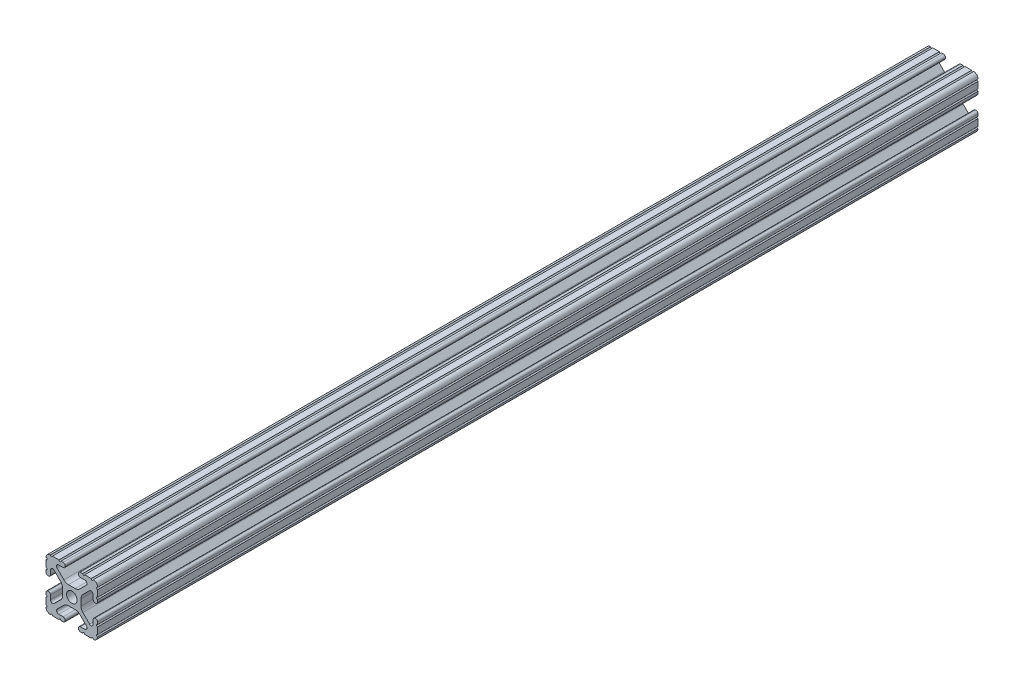
SolidWorks part; units mm, degrees
ref_plane "Front Plane" through (0, 0, 0) normal (0, 0, 1) x (1, 0, 0)
ref_plane "Top Plane" through (0, 0, 0) normal (0, 1, 0) x (1, 0, 0)
ref_plane "Right Plane" through (0, 0, 0) normal (1, 0, 0) x (0, 0, -1)
sketch "Sketch1" plane through (0, 0, 0) normal (0, 0, 1) x (1, 0, 0)
  line L88 (-7.1797, -8.6452) -> (-3.9523, -5.4237)
  line L89 (-1.7093, -4.4958) -> (1.7093, -4.4958)
  line L90 (3.9523, -5.4237) -> (7.1797, -8.6452)
  line L91 (6.4164, -10.4902) -> (4.2875, -10.4902)
  line L92 (3.2385, -11.5392) -> (3.2385, -11.651)
  line L93 (4.2875, -12.7) -> (5.3171, -12.7)
  line L94 (6.3331, -12.7) -> (9.5504, -12.7)
  line L95 (12.7, -9.5504) -> (12.7, -6.3331)
  line L96 (12.7, -5.3171) -> (12.7, -4.2875)
  line L97 (11.651, -3.2385) -> (11.5392, -3.2385)
  line L98 (10.4902, -4.2875) -> (10.4902, -6.4021)
  line L99 (8.7371, -7.1294) -> (5.441, -3.8408)
  line L100 (4.5085, -1.5932) -> (4.5085, 1.5932)
  line L101 (5.441, 3.8408) -> (8.7371, 7.1294)
  line L102 (10.4902, 6.4021) -> (10.4902, 4.2875)
  line L103 (11.5392, 3.2385) -> (11.651, 3.2385)
  line L104 (12.7, 4.2875) -> (12.7, 5.3171)
  line L105 (12.7, 6.3331) -> (12.7, 9.5504)
  line L106 (9.5504, 12.7) -> (6.3331, 12.7)
  line L107 (5.3171, 12.7) -> (4.2875, 12.7)
  line L108 (3.2385, 11.651) -> (3.2385, 11.5392)
  line L109 (4.2875, 10.4902) -> (6.4768, 10.4902)
  line L110 (7.207, 8.7244) -> (3.8983, 5.4232)
  line L111 (1.6558, 4.4958) -> (-1.6558, 4.4958)
  line L112 (-3.8983, 5.4232) -> (-7.207, 8.7244)
  line L113 (-6.4768, 10.4902) -> (-4.2875, 10.4902)
  line L114 (-3.2385, 11.5392) -> (-3.2385, 11.651)
  line L115 (-4.2875, 12.7) -> (-5.3171, 12.7)
  line L116 (-6.3331, 12.7) -> (-9.5504, 12.7)
  line L117 (-12.7, 9.5504) -> (-12.7, 6.3331)
  line L118 (-12.7, 5.3171) -> (-12.7, 4.2875)
  line L119 (-11.651, 3.2385) -> (-11.5392, 3.2385)
  line L120 (-10.4902, 4.2875) -> (-10.4902, 6.4021)
  line L121 (-8.7371, 7.1294) -> (-5.441, 3.8408)
  line L122 (-4.5085, 1.5932) -> (-4.5085, -1.5932)
  line L123 (-5.441, -3.8408) -> (-8.7371, -7.1294)
  line L124 (-10.4902, -6.4021) -> (-10.4902, -4.2875)
  line L125 (-11.5392, -3.2385) -> (-11.651, -3.2385)
  line L126 (-12.7, -4.2875) -> (-12.7, -5.3171)
  line L127 (-12.7, -6.3331) -> (-12.7, -9.5504)
  line L128 (-9.5504, -12.7) -> (-6.3331, -12.7)
  line L129 (-5.3171, -12.7) -> (-4.2875, -12.7)
  line L130 (-3.2385, -11.651) -> (-3.2385, -11.5392)
  line L131 (-4.2875, -10.4902) -> (-6.4164, -10.4902)
  circle A1 centre (0, 0) radius 2.6035
  arc A104 (-7.1797, -8.6452) -> (-6.4164, -10.4902) centre (-6.4164, -9.4098) ccw
  arc A105 (-1.7093, -4.4958) -> (-3.9523, -5.4237) centre (-1.7093, -7.6708) ccw
  arc A106 (3.9523, -5.4237) -> (1.7093, -4.4958) centre (1.7093, -7.6708) ccw
  arc A107 (6.4164, -10.4902) -> (7.1797, -8.6452) centre (6.4164, -9.4098) ccw
  arc A108 (4.2875, -10.4902) -> (3.2385, -11.5392) centre (4.2875, -11.5392) ccw
  arc A109 (3.2385, -11.651) -> (4.2875, -12.7) centre (4.2875, -11.651) ccw
  arc A110 (6.3331, -12.7) -> (5.3171, -12.7) centre (5.8251, -12.7) ccw
  arc A111 (10.5664, -12.6998) -> (9.5504, -12.7) centre (10.0584, -12.7) ccw
  arc A112 (10.5664, -12.6998) -> (12.6998, -10.5664) centre (10.5918, -10.5918) ccw
  arc A113 (12.7, -9.5504) -> (12.6998, -10.5664) centre (12.7, -10.0584) ccw
  arc A114 (12.7, -5.3171) -> (12.7, -6.3331) centre (12.7, -5.8251) ccw
  arc A115 (12.7, -4.2875) -> (11.651, -3.2385) centre (11.651, -4.2875) ccw
  arc A116 (11.5392, -3.2385) -> (10.4902, -4.2875) centre (11.5392, -4.2875) ccw
  arc A117 (8.7371, -7.1294) -> (10.4902, -6.4021) centre (9.4628, -6.4021) ccw
  arc A118 (4.5085, -1.5932) -> (5.441, -3.8408) centre (7.6835, -1.5932) ccw
  arc A119 (5.441, 3.8408) -> (4.5085, 1.5932) centre (7.6835, 1.5932) ccw
  arc A120 (10.4902, 6.4021) -> (8.7371, 7.1294) centre (9.4628, 6.4021) ccw
  arc A121 (10.4902, 4.2875) -> (11.5392, 3.2385) centre (11.5392, 4.2875) ccw
  arc A122 (11.651, 3.2385) -> (12.7, 4.2875) centre (11.651, 4.2875) ccw
  arc A123 (12.7, 6.3331) -> (12.7, 5.3171) centre (12.7, 5.8251) ccw
  arc A124 (12.6998, 10.5664) -> (12.7, 9.5504) centre (12.7, 10.0584) ccw
  arc A125 (12.6998, 10.5664) -> (10.5664, 12.6998) centre (10.5918, 10.5918) ccw
  arc A126 (9.5504, 12.7) -> (10.5664, 12.6998) centre (10.0584, 12.7) ccw
  arc A127 (5.3171, 12.7) -> (6.3331, 12.7) centre (5.8251, 12.7) ccw
  arc A128 (4.2875, 12.7) -> (3.2385, 11.651) centre (4.2875, 11.651) ccw
  arc A129 (3.2385, 11.5392) -> (4.2875, 10.4902) centre (4.2875, 11.5392) ccw
  arc A130 (7.207, 8.7244) -> (6.4768, 10.4902) centre (6.4768, 9.4563) ccw
  arc A131 (1.6558, 4.4958) -> (3.8983, 5.4232) centre (1.6558, 7.6708) ccw
  arc A132 (-3.8983, 5.4232) -> (-1.6558, 4.4958) centre (-1.6558, 7.6708) ccw
  arc A133 (-6.4768, 10.4902) -> (-7.207, 8.7244) centre (-6.4768, 9.4563) ccw
  arc A134 (-4.2875, 10.4902) -> (-3.2385, 11.5392) centre (-4.2875, 11.5392) ccw
  arc A135 (-3.2385, 11.651) -> (-4.2875, 12.7) centre (-4.2875, 11.651) ccw
  arc A136 (-6.3331, 12.7) -> (-5.3171, 12.7) centre (-5.8251, 12.7) ccw
  arc A137 (-10.5664, 12.6998) -> (-9.5504, 12.7) centre (-10.0584, 12.7) ccw
  arc A138 (-10.5664, 12.6998) -> (-12.6998, 10.5664) centre (-10.5918, 10.5918) ccw
  arc A139 (-12.7, 9.5504) -> (-12.6998, 10.5664) centre (-12.7, 10.0584) ccw
  arc A140 (-12.7, 5.3171) -> (-12.7, 6.3331) centre (-12.7, 5.8251) ccw
  arc A141 (-12.7, 4.2875) -> (-11.651, 3.2385) centre (-11.651, 4.2875) ccw
  arc A142 (-11.5392, 3.2385) -> (-10.4902, 4.2875) centre (-11.5392, 4.2875) ccw
  arc A143 (-8.7371, 7.1294) -> (-10.4902, 6.4021) centre (-9.4628, 6.4021) ccw
  arc A144 (-4.5085, 1.5932) -> (-5.441, 3.8408) centre (-7.6835, 1.5932) ccw
  arc A145 (-5.441, -3.8408) -> (-4.5085, -1.5932) centre (-7.6835, -1.5932) ccw
  arc A146 (-10.4902, -6.4021) -> (-8.7371, -7.1294) centre (-9.4628, -6.4021) ccw
  arc A147 (-10.4902, -4.2875) -> (-11.5392, -3.2385) centre (-11.5392, -4.2875) ccw
  arc A148 (-11.651, -3.2385) -> (-12.7, -4.2875) centre (-11.651, -4.2875) ccw
  arc A149 (-12.7, -6.3331) -> (-12.7, -5.3171) centre (-12.7, -5.8251) ccw
  arc A150 (-12.6998, -10.5664) -> (-12.7, -9.5504) centre (-12.7, -10.0584) ccw
  arc A151 (-12.6998, -10.5664) -> (-10.5664, -12.6998) centre (-10.5918, -10.5918) ccw
  arc A152 (-9.5504, -12.7) -> (-10.5664, -12.6998) centre (-10.0584, -12.7) ccw
  arc A153 (-5.3171, -12.7) -> (-6.3331, -12.7) centre (-5.8251, -12.7) ccw
  arc A154 (-4.2875, -12.7) -> (-3.2385, -11.651) centre (-4.2875, -11.651) ccw
  arc A155 (-3.2385, -11.5392) -> (-4.2875, -10.4902) centre (-4.2875, -11.5392) ccw
extrude "Boss-Extrude1" add sketch "Sketch1" along normal mid plane 609.6
sketch "Sketch2" plane through (0, 0, 304.8) normal (0, 0, 1) x (1, 0, 0)
  line L1 (-23.8111, 23.3739) -> (26.1662, 23.3739)
  line L2 (-23.8111, 23.3739) -> (-23.8111, -23.6266)
  line L3 (-23.8111, -23.6266) -> (26.1662, -23.6266)
  line L4 (26.1662, 23.3739) -> (26.1662, -23.6266)
extrude "Cut-Extrude1" cut sketch "Sketch2" against normal blind 176.53
